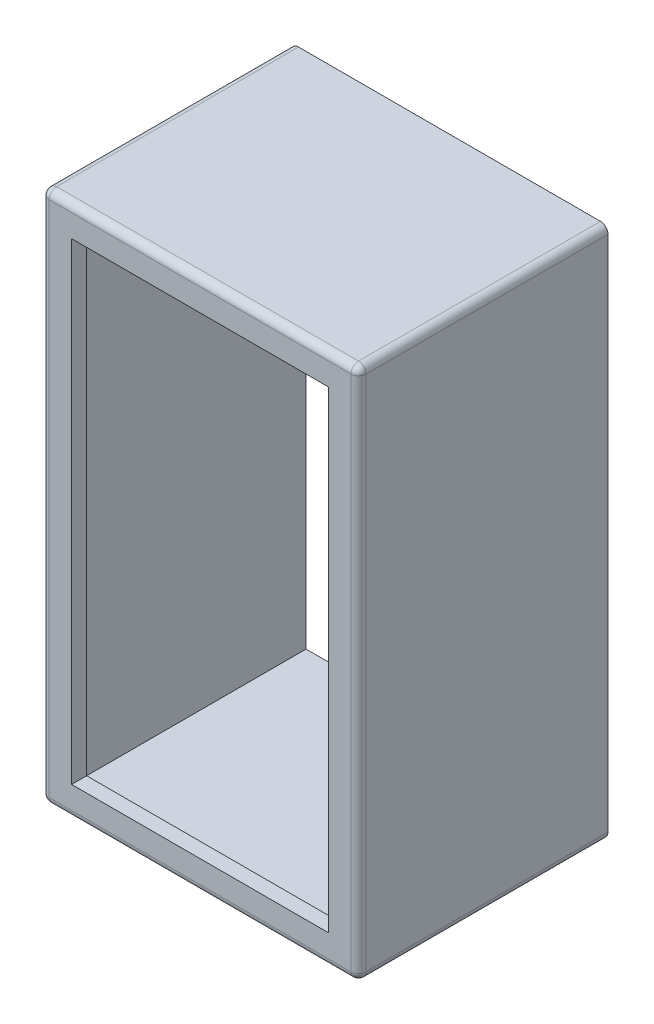
SolidWorks part; units mm, degrees
material "Nylon 101"
ref_plane "Front Plane" through (0, 0, 0) normal (0, 0, 1) x (1, 0, 0)
ref_plane "Top Plane" through (0, 0, 0) normal (0, 1, 0) x (1, 0, 0)
ref_plane "Right Plane" through (0, 0, 0) normal (1, 0, 0) x (0, 0, -1)
sketch "Sketch1" plane through (0, 0, 0) normal (0, 0, 1) x (1, 0, 0)
  line L1 (8.9229, 51.2767) -> (20.4164, 51.2767) construction
  line L2 (8.9229, 51.2767) -> (8.9229, 32.4807) construction
  line L3 (8.9229, 32.4807) -> (20.4164, 32.4807) construction
  line L4 (20.4164, 51.2767) -> (20.4164, 32.4807) construction
  line L7 (9.3039, 50.8957) -> (20.0354, 50.8957)
  line L8 (20.0354, 50.8957) -> (20.0354, 32.8617)
  line L9 (9.3039, 32.8617) -> (20.0354, 32.8617)
  line L10 (9.3039, 50.8957) -> (9.3039, 32.8617)
  point P4 (12.7998, 41.6606)
  dimension "D1" = 0.381
extrude "Boss-Extrude1" add sketch "Sketch1" along normal blind 7.9375
shell "Shell1" thickness 0.508
sketch "Sketch2" plane through (0, 0, 7.9375) normal (0, 0, 1) x (1, 0, 0)
  line L5 (9.8119, 50.3877) -> (9.8119, 33.3697)
  line L6 (19.5274, 50.3877) -> (9.8119, 50.3877)
  line L7 (19.5274, 33.3697) -> (19.5274, 50.3877)
  line L8 (9.8119, 33.3697) -> (19.5274, 33.3697)
  line L9 (9.8119, 50.3877) -> (9.8119, 33.3697)
  line L10 (19.5274, 50.3877) -> (9.8119, 50.3877)
  line L11 (19.5274, 33.3697) -> (19.5274, 50.3877)
  line L12 (9.8119, 33.3697) -> (19.5274, 33.3697)
  dimension "D1" = 0
extrude "Extrude-Thin1" add sketch "Sketch2" along normal blind 0.508 thin thin type mid plane wall 1.016
fillet "Fillet2" radius 0.254 8 edges at (9.3039, 50.8957, 4.2227) (20.0354, 50.8957, 4.2227) (20.0354, 32.8617, 4.2227) (9.3039, 32.8617, 4.2227) (14.6696, 32.8617, 8.4455) (14.6696, 50.8957, 8.4455) (20.0354, 41.8787, 8.4455) (9.3039, 41.8787, 8.4455)
